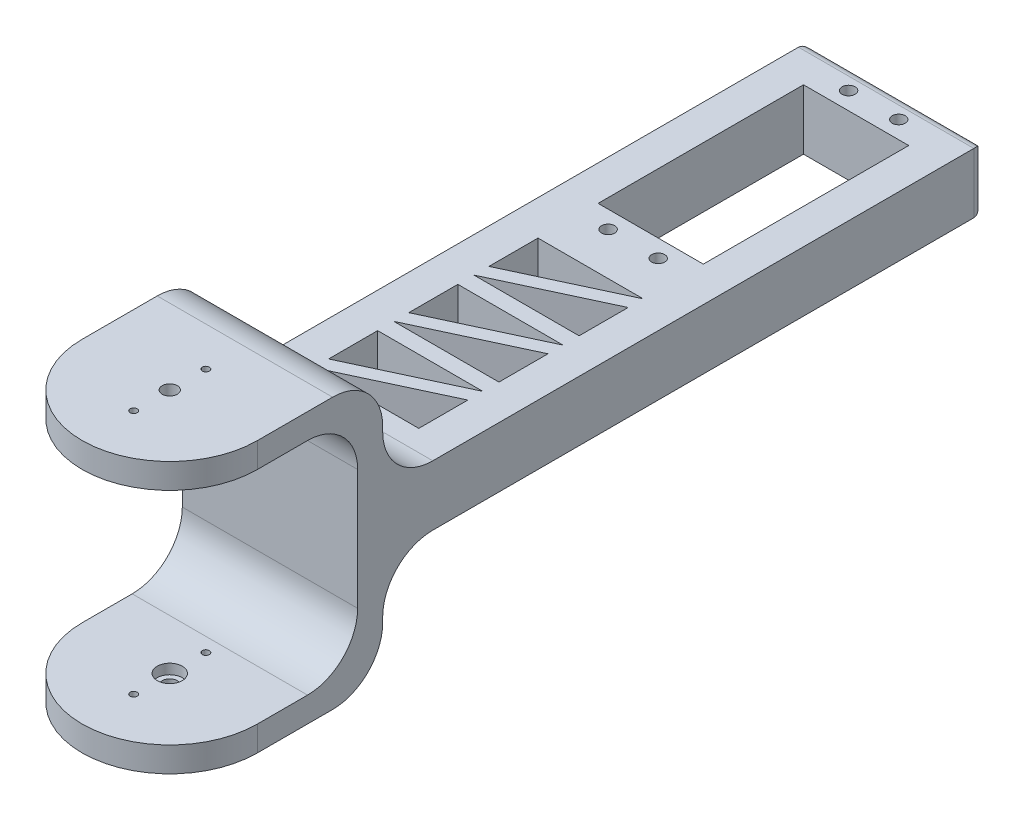
SolidWorks part; units mm, degrees
ref_plane "Front Plane" through (0, 0, 0) normal (0, 0, 1) x (1, 0, 0)
ref_plane "Top Plane" through (0, 0, 0) normal (0, 1, 0) x (1, 0, 0)
ref_plane "Right Plane" through (0, 0, 0) normal (1, 0, 0) x (0, 0, -1)
sketch "Sketch1" plane through (0, 0, 0) normal (0, 1, 0) x (1, 0, 0)
  line L2 (-17.5, 0) -> (-17.5, 20)
  line L3 (-17.5, 20) -> (17.5, 20)
  line L4 (17.5, 0) -> (17.5, 20)
  circle A0 centre (0, 0) radius 17.5
  circle A1 centre (0, 0) radius 1.5
  dimension "D1" = 35
  dimension "D2" = 3
  dimension "D3" = 20
  dimension "D4" = 35
extrude "Boss-Extrude1" add sketch "Sketch1" along normal blind 5 contours A0 A1 | A0 L4 L3 L2
ref_plane "Plane1" through (0, -49, 0) normal (0, 1, 0) x (1, 0, 0)
sketch "Sketch3" plane through (0, -49, 0) normal (0, 1, 0) x (1, 0, 0)
  line L3 (17.5, 0) -> (17.5, 20)
  line L4 (17.5, 20) -> (-17.5, 20)
  line L5 (-17.5, 20) -> (-17.5, 0)
  line L6 (17.5, 0) -> (17.5, 20)
  line L7 (17.5, 20) -> (-17.5, 20)
  line L8 (-17.5, 20) -> (-17.5, 0)
  circle A0 centre (0, 0) radius 1.5 construction
  arc A1 (-17.5, 0) -> (17.5, 0) centre (0, 0) ccw
  arc A2 (-17.5, 0) -> (17.5, 0) centre (0, 0) ccw
  circle A3 centre (0, 0) radius 1.5
  dimension "D1" = 0
extrude "Boss-Extrude2" add sketch "Sketch3" along normal blind 5 separate body
sketch "Sketch4" plane through (0, 0, -20) normal (0, 0, -1) x (-1, 0, 0)
  line L0 (19.25, -49) -> (-19.25, -49) construction
  line L1 (-17.5, 5) -> (17.5, 5)
  line L2 (-17.5, 5) -> (-17.5, -49)
  line L3 (-17.5, -49) -> (17.5, -49)
  line L4 (17.5, 5) -> (17.5, -49)
  line L5 (17.5, -44) -> (17.5, -49) construction
extrude "Boss-Extrude3" add sketch "Sketch4" along normal blind 5
fillet "Fillet1" radius 10 4 edges at (0, -49, -25) (0, 5, -25) (0, -44, -20) (0, 0, -20)
sketch "Sketch6" plane through (0, 0, -25) normal (0, 0, -1) x (-1, 0, 0)
  line L0 (-17.5, -5) -> (-17.5, -39) construction
  line L1 (-17.5, -16) -> (17.5, -16)
  line L2 (-17.5, -16) -> (-17.5, -28)
  line L3 (-17.5, -28) -> (17.5, -28)
  line L4 (17.5, -16) -> (17.5, -28)
  line L5 (17.5, -39) -> (17.5, -5) construction
  line L6 (17.5, -5) -> (-17.5, -5) construction
  line L7 (-17.5, -39) -> (17.5, -39) construction
  dimension "D1" = 11
  dimension "D2" = 11
extrude "Boss-Extrude4" add sketch "Sketch6" along normal blind 120
sketch "Sketch7" plane through (0, -16, 0) normal (0, 1, 0) x (1, 0, 0)
  line L0 (-17.5, 145) -> (17.5, 145) construction
  line L1 (-10.5, 137) -> (10.5, 137)
  line L2 (-10.5, 137) -> (-10.5, 96)
  line L3 (-10.5, 96) -> (10.5, 96)
  line L4 (10.5, 137) -> (10.5, 96)
  line L5 (17.5, 145) -> (17.5, 25) construction
  line L6 (0, 151.0886) -> (0, 78.4667) construction
  line L7 (-21.8229, 116.5) -> (22.9186, 116.5) construction
  circle A0 centre (-5, 140.5) radius 1.3
  circle A1 centre (5, 140.5) radius 1.3
  circle A2 centre (5, 92.5) radius 1.3
  circle A3 centre (-5, 92.5) radius 1.3
  dimension "D5" = 2.6
  dimension "D1" = 8
  dimension "D2" = 21
  dimension "D3" = 41
  dimension "D4" = 7
  dimension "D6" = 3.5
  dimension "D7" = 5
extrude "Cut-Extrude1" cut sketch "Sketch7" against normal up to next
sketch "Sketch8" plane through (0, -16, 0) normal (0, 1, 0) x (1, 0, 0)
  line L0 (-17.5, 145) -> (-17.5, 25) construction
  line L1 (-10.5, 84) -> (10.5, 84)
  line L2 (-10.5, 84) -> (-10.5, 32)
  line L3 (-10.5, 32) -> (10.5, 32)
  line L4 (10.5, 84) -> (10.5, 32)
  line L5 (17.5, 145) -> (17.5, 25) construction
  line L6 (-17.5, 25) -> (17.5, 25) construction
  line L7 (-10.5, 96) -> (10.5, 96) construction
  line L8 (-10.5, 74.2075) -> (10.5, 84)
  line L9 (-10.5, 71.2075) -> (10.5, 81)
  line L10 (-10.5, 71.2075) -> (10.5, 71.2075)
  dimension "D1" = 7
  dimension "D2" = 7
  dimension "D3" = 7
  dimension "D4" = 12
  dimension "D5" = 25
  dimension "D6" = 3
extrude "Cut-Extrude2" cut sketch "Sketch8" against normal up to next (12 mm away) contours L2 L8 L1 | L9 L10 L4
pattern_linear "LPattern1" count 3 spacing 16 along (0, 0, 1) of "Cut-Extrude2"
fillet "Fillet2" radius 10 2 edges at (0, -16, -25) (0, -28, -25)
fillet "Fillet3" radius 2 4 edges at (17.5, -22, -145) (-17.5, -22, -145) (0, -16, -145) (0, -28, -145)
sketch "Sketch11" plane through (0, 5, 0) normal (0, 1, 0) x (1, 0, 0)
  line L0 (0, 1.5) -> (0, -1.5) construction
  line L1 (0, -1.5) -> (-1.5, 0) construction
  line L2 (-1.5, 0) -> (1.5, 0) construction
  circle A0 centre (0, 7.2) radius 0.7
  circle A1 centre (0, 0) radius 1.5 construction
  circle A2 centre (0, 0) radius 1.5
  circle A3 centre (0, -7.2) radius 0.7
  dimension "D1" = 1.4
  dimension "D2" = 7.2
extrude "Cut-Extrude3" cut sketch "Sketch11" against normal through all contours A2 | A0 | A3
sketch "Sketch12" plane through (0, 0, 0) normal (0, -1, 0) x (1, 0, 0)
  circle A0 centre (0, 0) radius 2.5
  dimension "D1" = 5
extrude "Cut-Extrude4" cut sketch "Sketch12" against normal blind 2
sketch "Sketch13" plane through (0, -44, 0) normal (0, 1, 0) x (1, 0, 0)
  circle A0 centre (0, 0) radius 2.5
  dimension "D1" = 5
extrude "Cut-Extrude5" cut sketch "Sketch13" against normal blind 2
